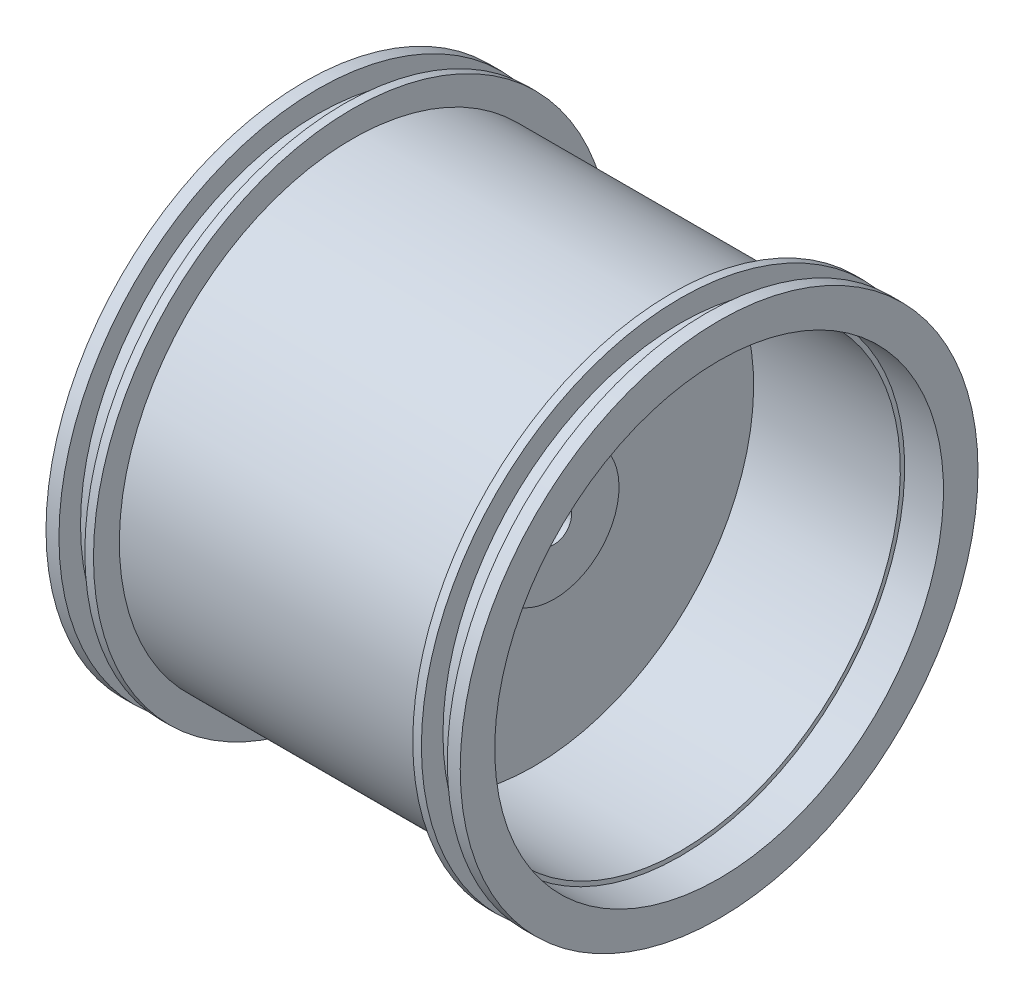
SolidWorks part; units mm, degrees
ref_plane "Alzado" through (0, 0, 0) normal (0, 0, 1) x (1, 0, 0)
ref_plane "Planta" through (0, 0, 0) normal (0, 1, 0) x (1, 0, 0)
ref_plane "Vista lateral" through (0, 0, 0) normal (1, 0, 0) x (0, 0, -1)
sketch "Croquis1" plane through (0, 0, 0) normal (0, 0, 1) x (1, 0, 0)
  line L0 (0, 0) -> (-2.5, 0) construction
  line L1 (2.5, 0) -> (4.9, 0) construction
  line L2 (4.9, 0) -> (4.9, 7.5)
  line L3 (2.5, 0) -> (0, 0) construction
  line L4 (4.9, 7.5) -> (2.5, 7.5)
  line L5 (2.5, 7.5) -> (2.5, 25.5)
  line L6 (2.5, 25.5) -> (19.5, 25.5)
  line L7 (19.5, 25.5) -> (19.5, 26)
  line L8 (19.5, 26) -> (24, 26)
  line L9 (24, 26) -> (24, 30)
  line L10 (24, 30) -> (22.5, 30)
  line L11 (22.5, 30) -> (22.5, 27.5)
  line L12 (22.5, 27.5) -> (19.5, 27.5)
  line L13 (19.5, 27.5) -> (19.5, 30)
  line L14 (19.5, 30) -> (18.5, 30)
  line L15 (18.5, 30) -> (18.5, 27)
  line L16 (18.5, 27) -> (-18.5, 27)
  line L17 (0, 27) -> (0, 0) construction
  line L18 (-19.5, 25.5) -> (-19.5, 26)
  line L19 (-19.5, 26) -> (-24, 26)
  line L20 (-24, 26) -> (-24, 30)
  line L21 (-24, 30) -> (-22.5, 30)
  line L22 (-22.5, 30) -> (-22.5, 27.5)
  line L23 (-19.5, 27.5) -> (-19.5, 30)
  line L24 (-22.5, 27.5) -> (-19.5, 27.5)
  line L25 (-19.5, 30) -> (-18.5, 30)
  line L26 (-18.5, 30) -> (-18.5, 27)
  line L27 (-2.5, 25.5) -> (-19.5, 25.5)
  line L28 (-2.5, 7.5) -> (-2.5, 25.5)
  line L29 (-2.5, 7.5) -> (-2.5, 0)
  line L30 (-2.5, 0) -> (-2.5, 7.5)
  line L31 (-2.5, 0) -> (4.9, 0)
  dimension "D1" = 5
  dimension "D2" = 25.5
  dimension "D3" = 7.5
  dimension "D4" = 2.4
  dimension "D5" = 17
  dimension "D6" = 30
  dimension "D7" = 4
  dimension "D8" = 1.5
  dimension "D9" = 1.5
  dimension "D10" = 1
  dimension "D11" = 1.5
  dimension "D12" = 24
  dimension "D13" = 4.5
revolve "Revolución1" add sketch "Croquis1" angle 360 about L31
sketch "Croquis2" plane through (4.9, 0, 0) normal (1, 0, 0) x (0, 0, -1)
  circle A0 centre (0, 0) radius 2
  dimension "D1" = 4
extrude "Cortar-Extruir1" cut sketch "Croquis2" against normal up to next
sketch "Croquis3" plane through (-2.5, 0, 0) normal (-1, 0, 0) x (0, 0, 1)
  line L1 (0, 8.2561) -> (-7.15, 4.1281)
  line L2 (-7.15, 4.1281) -> (-7.15, -4.1281)
  line L3 (-7.15, -4.1281) -> (0, -8.2561)
  line L4 (0, -8.2561) -> (7.15, -4.1281)
  line L5 (7.15, -4.1281) -> (7.15, 4.1281)
  line L6 (7.15, 4.1281) -> (0, 8.2561)
  circle A0 centre (0, 0) radius 7.15 construction
  circle A1 centre (0, 0) radius 2 construction
  circle A2 centre (0, 0) radius 2
  dimension "D1" = 14.3
extrude "Saliente-Extruir1" add sketch "Croquis3" along normal blind 6.6
sketch "Croquis4" plane through (-9.1, 0, 0) normal (-1, 0, 0) x (0, 0, 1)
  line L0 (6.15, 3.5507) -> (0, 7.1014)
  line L1 (0, 7.1014) -> (-6.15, 3.5507)
  line L2 (-6.15, 3.5507) -> (-6.15, -3.5507)
  line L3 (-6.15, -3.5507) -> (0, -7.1014)
  line L4 (0, -7.1014) -> (6.15, -3.5507)
  line L5 (6.15, -3.5507) -> (6.15, 3.5507)
  line L6 (7.15, 4.1281) -> (0, 8.2561)
  line L7 (0, 8.2561) -> (-7.15, 4.1281)
  line L8 (-7.15, 4.1281) -> (-7.15, -4.1281)
  line L9 (-7.15, -4.1281) -> (0, -8.2561)
  line L10 (0, -8.2561) -> (7.15, -4.1281)
  line L11 (7.15, -4.1281) -> (7.15, 4.1281)
  line L12 (7.15, 4.1281) -> (0, 8.2561) construction
  line L13 (0, 8.2561) -> (-7.15, 4.1281) construction
  line L14 (-7.15, 4.1281) -> (-7.15, -4.1281) construction
  line L15 (-7.15, -4.1281) -> (0, -8.2561) construction
  line L16 (0, -8.2561) -> (7.15, -4.1281) construction
  line L17 (7.15, -4.1281) -> (7.15, 4.1281) construction
  dimension "D1" = 0
  dimension "D2" = 1
extrude "Cortar-Extruir2" cut sketch "Croquis4" against normal blind 4.2
